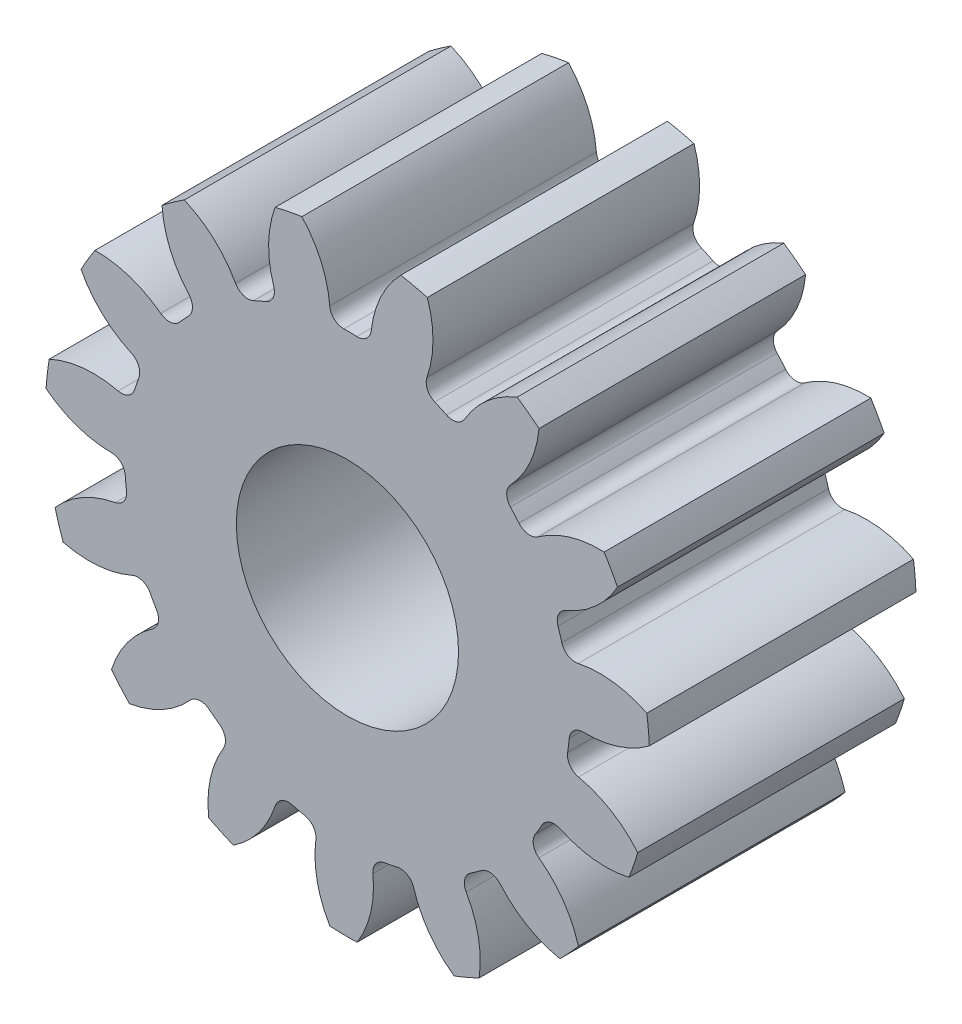
SolidWorks part; units mm, degrees
ref_plane "Front" through (0, 0, 0) normal (0, 0, 1) x (1, 0, 0)
ref_plane "Top" through (0, 0, 0) normal (0, 1, 0) x (1, 0, 0)
ref_plane "Right" through (0, 0, 0) normal (1, 0, 0) x (0, 0, -1)
sketch "Sketch3" plane through (0, 0, 0) normal (0, 0, 1) x (1, 0, 0)
  circle A0 centre (0, 0) radius 10.795
  dimension "od" = 21.59
extrude "gearBody" add sketch "Sketch3" along normal blind 9.525
sketch "Sketch2" plane through (0, 0, 0) normal (0, 0, 1) x (1, 0, 0)
  line L0 (0, 0) -> (8.5197, 3.529) construction
  line L1 (10.9941, -4.0771) -> (0, 0) construction
  line L2 (0, 0) -> (36.3143, 0) construction
  line L3 (9.5243, -0.1145) -> (9.2881, -2.1109) construction
  line L5 (9.4062, -1.1127) -> (0, 0) construction
  line L7 (0, 0) -> (9.2216, 0) construction
  arc A0 (9.2197, -0.1851) -> (9.0084, -1.9713) centre (0, 0) ccw construction
  arc A1 (10.7833, 0.5024) -> (10.3684, -3.0046) centre (0, 0) ccw construction
  arc A2 (9.5243, -0.1145) -> (9.2881, -2.1109) centre (0, 0) ccw construction
  arc A3 (7.8647, -1.163) -> (7.919, -0.7041) centre (0, 0) ccw
  arc A4 (10.9941, -4.0771) -> (8.2537, -1.724) centre (7.4611, -5.4194) ccw
  arc A5 (10.9941, -4.0771) -> (11.642, 1.3993) centre (0, 0) ccw
  arc A6 (11.642, 1.3993) -> (8.4282, -0.2494) centre (8.5197, 3.529) cw
  arc A7 (7.919, -0.7041) -> (8.4282, -0.2494) centre (8.4161, -0.7483) cw
  arc A8 (8.2537, -1.724) -> (7.8647, -1.163) centre (8.3584, -1.236) cw
  point P6 (11.642, 1.3993)
  point P22 (10.9941, -4.0771)
  dimension "baseDia" = 18.4432
  dimension "od" = 21.59
  dimension "pd" = 19.05
  dimension "rd" = 15.9004
  dimension "rFillet" = 0.4991
  dimension "pointX" = 11.642
  dimension "pointY" = 1.3993
  dimension "CTT" = 1.9964
  dimension "flankCenterAngle" = 22.5
extrude "toothCut" cut sketch "Sketch2" along normal through all
pattern_circular "CirPattern1" count 15 over 360 about axis through (0, 0, 0) along (0, 0, 1) of "toothCut"
sketch "hub1Dia" plane through (0, 0, 0) normal (0, 0, -1) x (-1, 0, 0)
  circle A0 centre (0, 0) radius 25.4
  dimension "hub1Dia" = 50.8
extrude "hub1" [suppressed] add sketch "hub1Dia" along normal blind 19.05
sketch "hub2Dia" plane through (0, 0, 9.525) normal (0, 0, 1) x (1, 0, 0)
  circle A0 centre (0, 0) radius 21.844
  dimension "hub2dia" = 43.688
extrude "hub2" [suppressed] add sketch "hub2Dia" along normal blind 16.002
sketch "boreDia" plane through (0, 0, 0) normal (0, 0, 1) x (1, 0, 0)
  circle A0 centre (0, 0) radius 3.9688
  dimension "boreDia" = 7.9375
extrude "bore" cut sketch "boreDia" against normal mid plane 25400
chamfer "hub2Chamfer" [suppressed] distance 0.508 angle 45
chamfer "hub2BoreChamfer" [suppressed] distance 0.508 angle 45
chamfer "hub1BoreChamfer" [suppressed] distance 0.508 angle 45
chamfer "hub1Chamfer" [suppressed] distance 0.508 angle 45
chamfer "BoreChamfer2" [suppressed] distance 0.508 angle 45
chamfer "boreChamfer1" [suppressed] distance 0.508 angle 45
